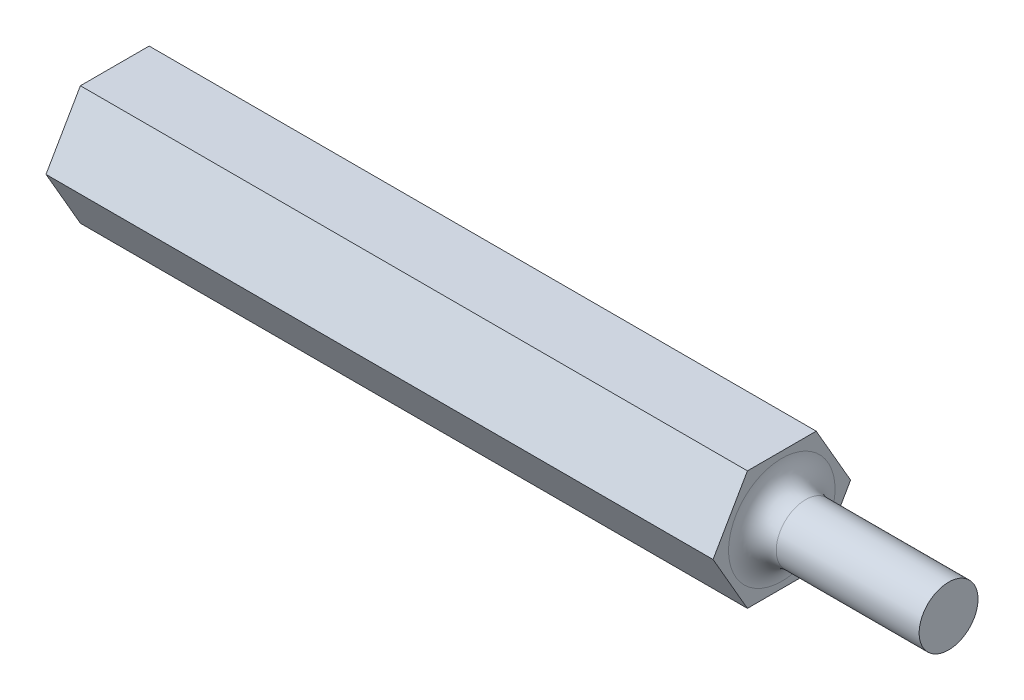
SolidWorks part; units mm, degrees
ref_plane "Front Plane" through (0, 0, 0) normal (0, 0, 1) x (1, 0, 0)
ref_plane "Top Plane" through (0, 0, 0) normal (0, 1, 0) x (1, 0, 0)
ref_plane "Right Plane" through (0, 0, 0) normal (1, 0, 0) x (0, 0, -1)
sketch "Sketch1" plane through (0, 0, 0) normal (1, 0, 0) x (0, 0, -1)
  line L0 (0, 55) -> (0, -55) construction
  line L1 (3.6662, -6.35) -> (7.3323, 0)
  line L2 (7.3323, 0) -> (3.6662, 6.35)
  line L3 (3.6662, 6.35) -> (-3.6662, 6.35)
  line L4 (-3.6662, 6.35) -> (-7.3323, 0)
  line L5 (-7.3323, 0) -> (-3.6662, -6.35)
  line L6 (-3.6662, -6.35) -> (3.6662, -6.35)
  circle A0 centre (0, 0) radius 6.35 construction
  dimension "D1" = 12.7
extrude "Boss-Extrude1" add sketch "Sketch1" along normal blind 88.9
sketch "Sketch2" plane through (88.9, 0, 0) normal (1, 0, 0) x (0, 0, -1)
  circle A0 centre (0, 0) radius 3.1369
  circle A1 centre (0, 0) radius 9.3995
  dimension "D1" = 6.2738
extrude "Cut-Extrude1" cut sketch "Sketch2" against normal blind 17.78
fillet "Fillet1" radius 2.54 1 edges at (71.12, 0, -3.1369)
